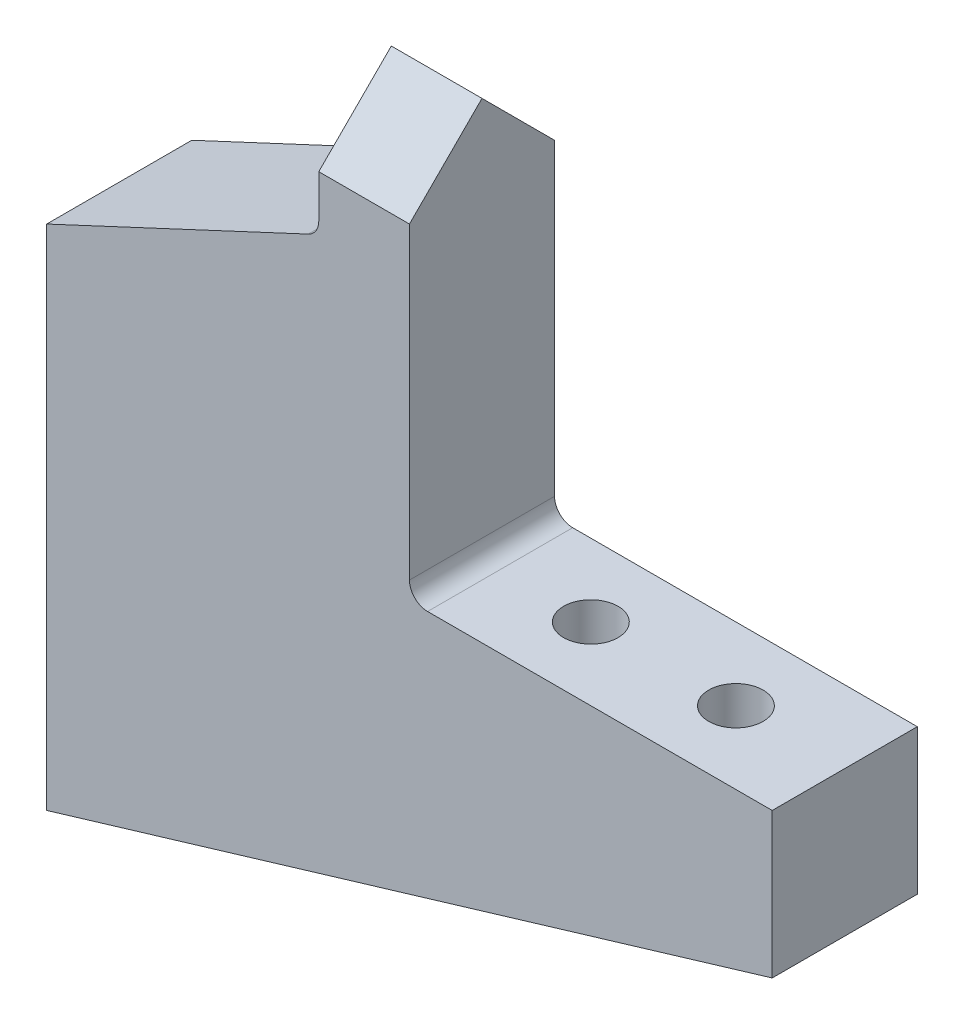
SolidWorks part; units mm, degrees
material "2024-T4"
ref_plane "正面" through (0, 0, 0) normal (0, 0, 1) x (1, 0, 0)
ref_plane "平面" through (0, 0, 0) normal (0, 1, 0) x (1, 0, 0)
ref_plane "右側面" through (0, 0, 0) normal (1, 0, 0) x (0, 0, -1)
sketch "Sketch1" plane through (0, 0, 0) normal (0, 0, 1) x (1, 0, 0)
  line L0 (0, 0) -> (0, 42)
  line L1 (0, 42) -> (20, 42)
  line L2 (20, 42) -> (20, 20)
  line L3 (20, 20) -> (40, 20)
  line L4 (40, 20) -> (40, 12)
  line L5 (40, 12) -> (0, 0)
  point P6 (30, 20)
  dimension "D1" = 22
  dimension "D2" = 20
  dimension "D3" = 20
  dimension "D4" = 8
  dimension "D5" = 42
extrude "Boss-Extrude1" add sketch "Sketch1" along normal blind 8
sketch "Sketch2" plane through (0, 0, 8) normal (0, 0, 1) x (1, 0, 0)
  line L0 (15, 42) -> (15, 35)
  line L1 (20, 42) -> (0, 42) construction
  line L2 (0, 42) -> (0, 0) construction
  line L3 (0, 28) -> (0, 42)
  line L4 (0, 42) -> (15, 42)
  line L5 (15, 35) -> (0, 28)
  dimension "D1" = 14
  dimension "D2" = 7
extrude "Cut-Extrude1" cut sketch "Sketch2" against normal blind 8
sketch "Sketch7" plane through (0, 20, 0) normal (0, 1, 0) x (1, 0, 0)
  line L1 (40, -8) -> (40, 0) construction
  circle A0 centre (34, -4) radius 1.5
  circle A1 centre (26, -4) radius 1.5
  dimension "D1" = 6
  dimension "D2" = 14
extrude "Cut-Extrude4" cut sketch "Sketch7" against normal blind 6
sketch "Sketch9" plane through (0, 14, 0) normal (0, 1, 0) x (1, 0, 0)
  circle A0 centre (34, -4) radius 2.5
  circle A1 centre (26, -4) radius 2.5
extrude "Cut-Extrude5" cut sketch "Sketch9" against normal through all
sketch "Sketch5" plane through (20, 0, 0) normal (1, 0, 0) x (0, 0, -1)
  line L0 (-8, 42) -> (-4, 42)
  line L1 (-8, 42) -> (0, 42) construction
  line L2 (-4, 42) -> (-8, 38)
  line L3 (-8, 20) -> (-8, 42) construction
  line L9 (-8, 42) -> (-8, 38)
  dimension "D1" = 4
  dimension "D2" = 4
extrude "Cut-Extrude2" cut sketch "Sketch5" against normal through all
sketch "Sketch6" plane through (20, 0, 0) normal (1, 0, 0) x (0, 0, -1)
  line L0 (0, 42) -> (-4, 42)
  line L1 (-4, 42) -> (0, 38)
  line L2 (0, 20) -> (0, 42) construction
  line L3 (0, 38) -> (0, 42)
  dimension "D1" = 4
extrude "Cut-Extrude3" cut sketch "Sketch6" against normal through all
hole_wizard "M2x0.4 Tapped Hole1" positions "3DSketch1" profile "Sketch10" tap size "M2x0.4" standard "JIS"
sketch3d "3DSketch1"
  line L0 (0, 28, 0) -> (0, 28, 8) construction
  line L1 (0, 28, 0) -> (0, 0, 0) construction
  point P0 (0, 24, 4)
  point P2 (0, 16, 4)
  point P4 (0, 8, 4)
  dimension "D1" = 4
  dimension "D2" = 12
  dimension "D3" = 20
  dimension "D4" = 4
  dimension "D5" = 4
  dimension "D6" = 4
sketch "Sketch10" plane through (0, 24, 4) normal (0, 1, 0) x (0, 0, 1)
  line L0 (0, 0) -> (0, 8.4807)
  line L1 (0, 8.4807) -> (0.8, 8)
  line L2 (0.8, 8) -> (0.8, 0)
  line L5 (0.8, 0) -> (0, 0)
  line L10 (0, 8.4807) -> (-0.8, 8) construction
  line L11 (0, -6.35) -> (0, 107.95) construction
  dimension "Tap Drill Dia." = 1.6
  dimension "Tap Drill Depth" = 8
  dimension "Drill Angle" = 118
cosmetic thread "Hole Thread7" parameters "D1"=7, "D2"=2
cosmetic thread "Hole Thread8" parameters "D1"=7, "D2"=2
cosmetic thread "Hole Thread9" parameters "D1"=7, "D2"=2
fillet "Fillet1" radius 1 1 edges at (20, 20, 4)
fillet "Fillet2" radius 1 1 edges at (15, 35, 4)
